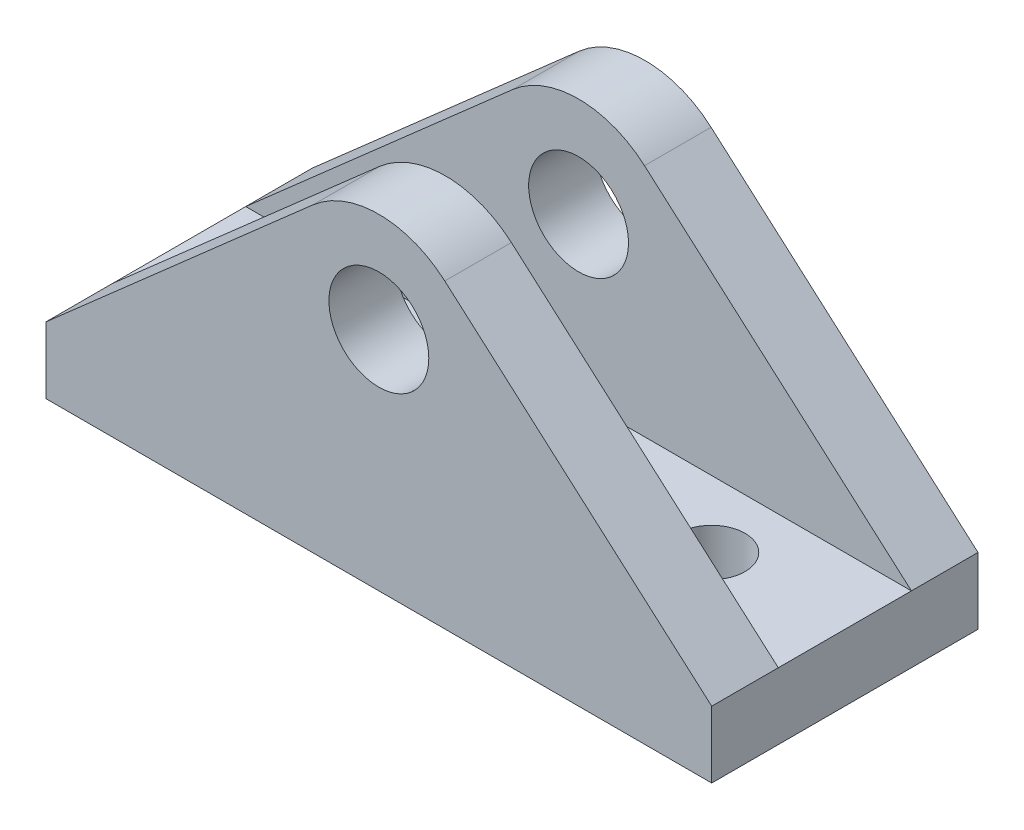
SolidWorks part; units mm, degrees
ref_plane "Front Plane" through (0, 0, 0) normal (0, 0, 1) x (1, 0, 0)
ref_plane "Top Plane" through (0, 0, 0) normal (0, 1, 0) x (1, 0, 0)
ref_plane "Right Plane" through (0, 0, 0) normal (1, 0, 0) x (0, 0, -1)
sketch "Sketch1" plane through (0, 0, 0) normal (0, 0, 1) x (1, 0, 0)
  line L0 (6.2906, 13.5022) -> (31.75, -8.89)
  line L1 (-31.75, -15.24) -> (31.75, -15.24)
  line L5 (-6.2906, 13.5022) -> (-31.75, -8.89)
  line L11 (31.75, -15.24) -> (-31.75, -15.24)
  line L12 (31.75, -15.24) -> (31.75, -8.89)
  line L13 (31.75, -8.89) -> (-31.75, -8.89)
  line L14 (-31.75, -15.24) -> (-31.75, -8.89)
  line L15 (0, 6.35) -> (0, -15.24) construction
  circle A0 centre (0, 6.35) radius 4.7625
  circle A1 centre (0, 6.35) radius 9.525
  point P0 (0, 0)
  point P6 (31.75, -12.7)
  point P7 (31.75, -2.6516)
  point P8 (0, 6.35)
extrude "Boss-Extrude1" add sketch "Sketch1" along normal blind 25.4
sketch "Sketch2" plane through (31.75, 0, 0) normal (1, 0, 0) x (0, 0, -1)
  line L0 (0, 0) -> (-6.35, 0)
  line L1 (-25.4, -8.89) -> (0, -8.89) construction
  line L6 (-6.35, 0) -> (-19.05, 0)
  line L7 (-6.35, 0) -> (-6.35, -8.89)
  line L8 (-6.35, -8.89) -> (-19.05, -8.89)
  line L9 (-19.05, 0) -> (-19.05, -8.89)
  line L11 (-6.35, 0) -> (-19.05, 0)
  line L12 (-6.35, 0) -> (-6.35, 18.3828)
  line L13 (-6.35, 18.3828) -> (-19.05, 18.3828)
  line L14 (-19.05, 0) -> (-19.05, 18.3828)
  line M12 (0, -8.89) -> (-25.4, -8.89)
extrude "Cut-Extrude1" cut sketch "Sketch2" against normal through all contours L6 L9 L7 M12 | L14 L6 L12 L13
sketch "Sketch3" plane through (0, -8.89, 0) normal (0, 1, 0) x (1, 0, 0)
  line L0 (0, 0) -> (0, -12.7)
  line L1 (-19.05, -12.7) -> (19.05, -12.7) construction
  circle A0 centre (-19.05, -12.7) radius 3.175
  circle A1 centre (19.05, -12.7) radius 3.175
  point P6 (0, -12.7)
extrude "Cut-Extrude2" cut sketch "Sketch3" against normal through all
